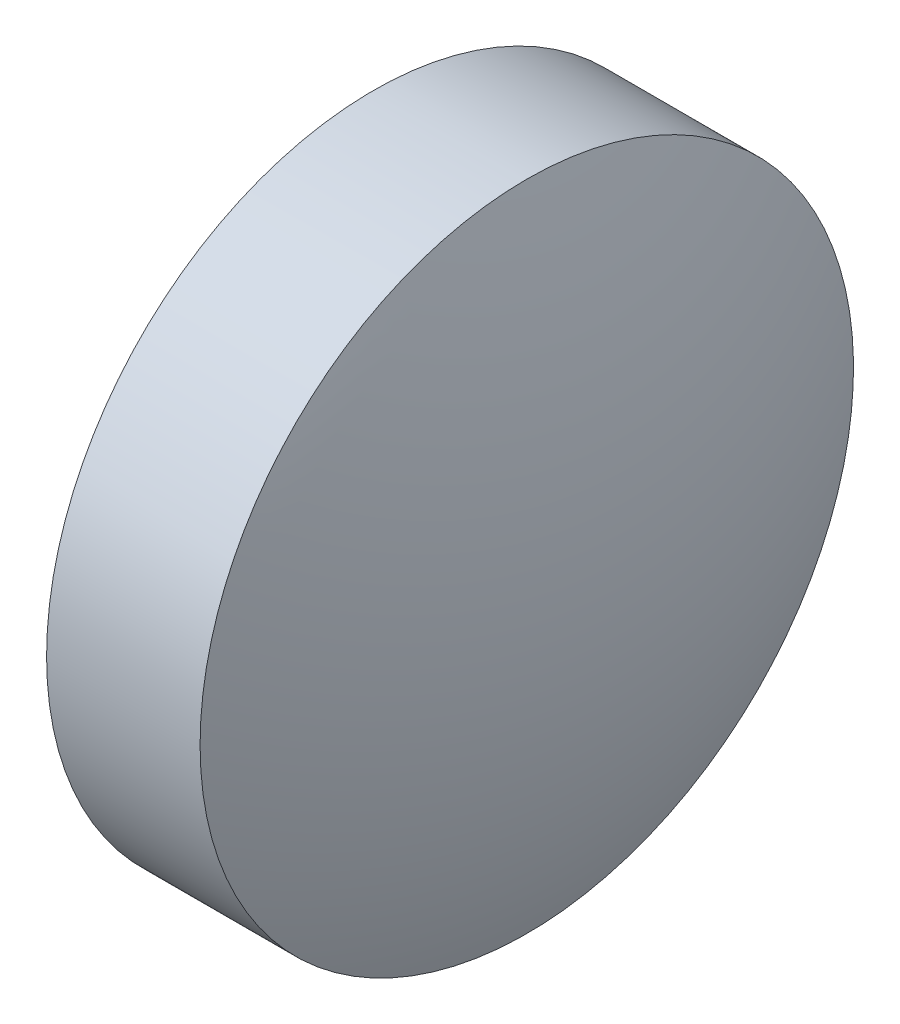
SolidWorks part; units mm, degrees
ref_plane "前视基准面" through (0, 0, 0) normal (0, 0, 1) x (1, 0, 0)
ref_plane "上视基准面" through (0, 0, 0) normal (0, 1, 0) x (1, 0, 0)
ref_plane "右视基准面" through (0, 0, 0) normal (1, 0, 0) x (0, 0, -1)
sketch "草图1" plane through (0, 0, 0) normal (0, 0, 1) x (1, 0, 0)
  line L0 (21.7331, 13.0042) -> (27.8685, 13.0042) construction
  line L1 (22.5947, 13.0042) -> (22.5947, 16.1542)
  line L2 (24.6947, 13.0042) -> (22.5947, 13.0042)
  line L5 (22.5947, 16.1542) -> (24.0747, 16.1542)
  arc A0 (24.6947, 13.0042) -> (24.0747, 16.1542) centre (16.3827, 13.0042) ccw
revolve "旋转1" add sketch "草图1" angle 360 about L0
